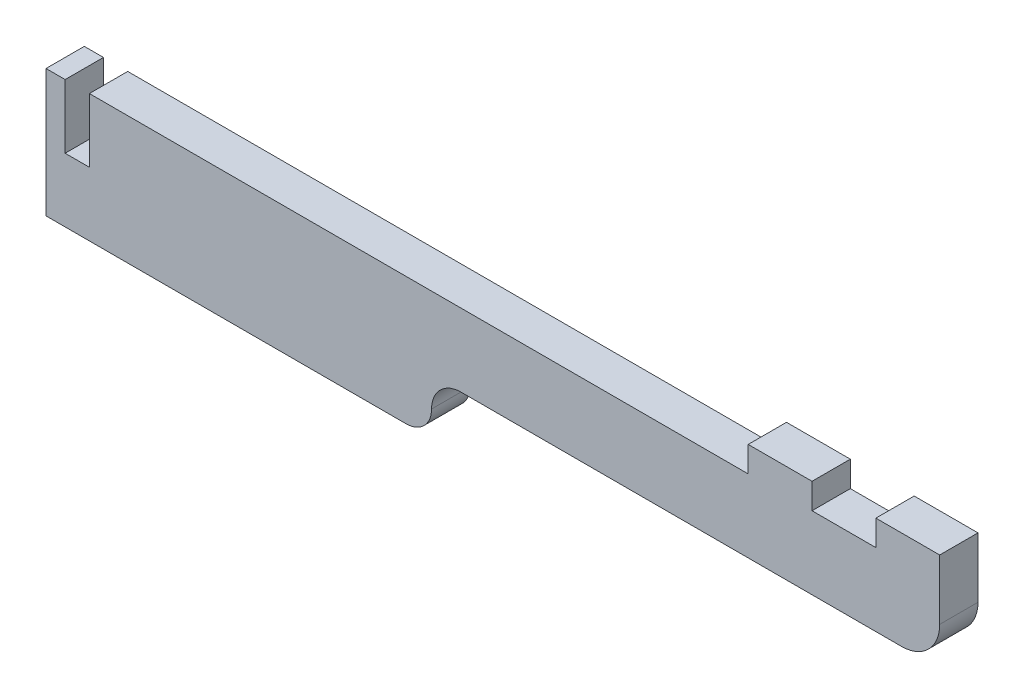
SolidWorks part; units mm, degrees
ref_plane "Ebene vorne" through (0, 0, 0) normal (0, 0, 1) x (1, 0, 0)
ref_plane "Ebene oben" through (0, 0, 0) normal (0, 1, 0) x (1, 0, 0)
ref_plane "Ebene rechts" through (0, 0, 0) normal (1, 0, 0) x (0, 0, -1)
sketch "Skizze1" plane through (0, 0, 0) normal (0, 0, 1) x (1, 0, 0)
  line L1 (0, 0) -> (140, 0)
  line L2 (0, 0) -> (0, 20)
  line L3 (0, 20) -> (140, 20)
  line L4 (140, 0) -> (140, 20)
  dimension "D1" = 20
  dimension "D2" = 140
extrude "Aufsatz-Linear austragen1" add sketch "Skizze1" along normal blind 6
sketch "Skizze2" plane through (0, 0, 0) normal (0, 0, -1) x (-1, 0, 0)
  line L0 (-140, 20) -> (0, 20) construction
  line L1 (-140, 20) -> (-130, 20)
  line L2 (-140, 20) -> (-140, 24)
  line L3 (-140, 24) -> (-130, 24)
  line L4 (-130, 20) -> (-130, 24)
  line L5 (-120, 20) -> (-110, 20)
  line L6 (-120, 20) -> (-120, 24)
  line L7 (-120, 24) -> (-110, 24)
  line L8 (-110, 20) -> (-110, 24)
  dimension "D1" = 4
  dimension "D2" = 10
  dimension "D3" = 10
extrude "Aufsatz-Linear austragen2" add sketch "Skizze2" against normal up to surface (6 mm away) up to face at (70, 10, 6)
sketch "Skizze3" plane through (0, 0, 0) normal (0, 0, -1) x (-1, 0, 0)
  line L0 (-3, 20) -> (-3, 10)
  line L1 (-110, 20) -> (0, 20) construction
  line L2 (-3, 10) -> (-6.8, 10)
  line L3 (-6.8, 10) -> (-6.8, 20)
  line L4 (-6.8, 20) -> (-3, 20)
  line L5 (0, 20) -> (0, 0) construction
  dimension "D1" = 3.8
  dimension "D2" = 3
  dimension "D3" = 10
extrude "Schnitt-Linear austragen1" cut sketch "Skizze3" against normal up to next
sketch "Skizze4" plane through (0, 0, 6) normal (0, 0, 1) x (1, 0, 0)
  line L0 (134.0158, 8.6) -> (65, 8.6)
  line L1 (140, 0) -> (140, 24) construction
  line L3 (0, 0) -> (140, 0) construction
  line L4 (56.4, 0) -> (140, 0)
  line L5 (140, 0) -> (140, 14.5842)
  arc A0 (134.0158, 8.6) -> (140, 14.5842) centre (134.0158, 14.5842) ccw
  arc A1 (60.4, 4) -> (65, 8.6) centre (65, 4) cw
  arc A2 (56.4, 0) -> (60.4, 4) centre (56.4, 4) ccw
  point P1 (0, 0)
  point P5 (56.2861, 3.5402)
  point P12 (0, 0)
  point P17 (53.2516, 0)
  point P18 (0, 0)
  dimension "D1" = 75
  dimension "D2" = 8.6
  dimension "D3" = 4
extrude "Schnitt-Linear austragen2" cut sketch "Skizze4" against normal up to next
